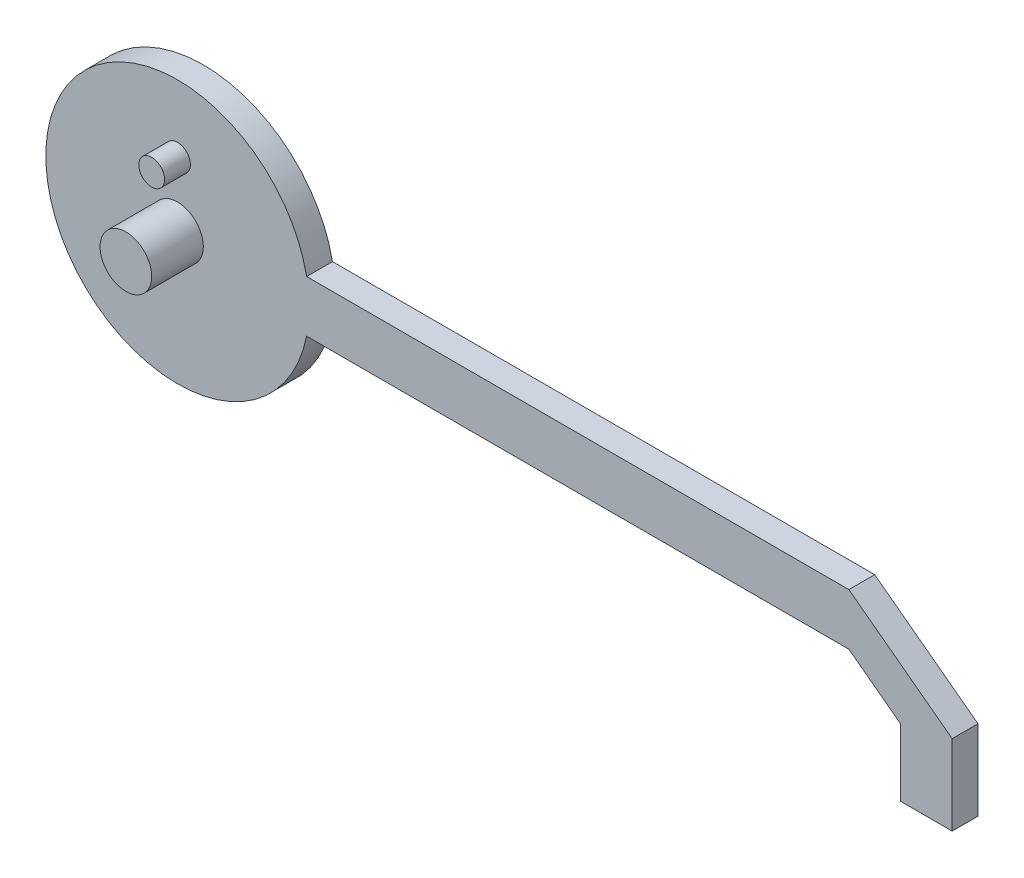
SolidWorks part; units mm, degrees
ref_plane "Alzado" through (0, 0, 0) normal (0, 0, 1) x (1, 0, 0)
ref_plane "Planta" through (0, 0, 0) normal (0, 1, 0) x (1, 0, 0)
ref_plane "Vista lateral" through (0, 0, 0) normal (1, 0, 0) x (0, 0, -1)
sketch "Croquis1" plane through (0, 0, 0) normal (0, 0, 1) x (1, 0, 0)
  line L0 (133.8574, 0) -> (1136.4137, 0) construction
  line L1 (-52.4975, 5) -> (52.4975, 5)
  line L2 (62.4975, -25.5) -> (72.4975, -25.5)
  line L3 (72.4975, -25.5) -> (72.4975, -10)
  line L4 (72.4975, -10) -> (52.4975, 5)
  line L5 (52.4975, -5) -> (62.4975, -12.5)
  line L6 (62.4975, -25.5) -> (62.4975, -12.5)
  line L7 (52.4975, -5) -> (-52.4975, -5)
  line L10 (-52.4975, 5) -> (52.4975, -5) construction
  arc A0 (-52.4975, 5) -> (-52.4975, -5) centre (-77.5025, 0) ccw
  point P10 (72.4975, -17.75)
  point P15 (0, 0)
  dimension "D1" = 51
  dimension "D2" = 5
  dimension "D3" = 150
  dimension "D4" = 10
  dimension "D5" = 10
  dimension "D6" = 25
extrude "Saliente-Extruir1" add sketch "Croquis1" along normal blind 5
sketch "Croquis2" plane through (0, 0, 5) normal (0, 0, 1) x (1, 0, 0)
  circle A1 centre (-77.5025, 0) radius 12.5 construction
  circle A2 centre (-77.5025, 12.5) radius 2.5
  dimension "D1" = 5
  dimension "D2" = 25
extrude "Saliente-Extruir2" add sketch "Croquis2" along normal blind 5
sketch "Croquis3" plane through (0, 0, 5) normal (0, 0, 1) x (1, 0, 0)
  circle A0 centre (-77.5025, 0) radius 5
  dimension "D1" = 10
extrude "Saliente-Extruir3" add sketch "Croquis3" along normal blind 10
